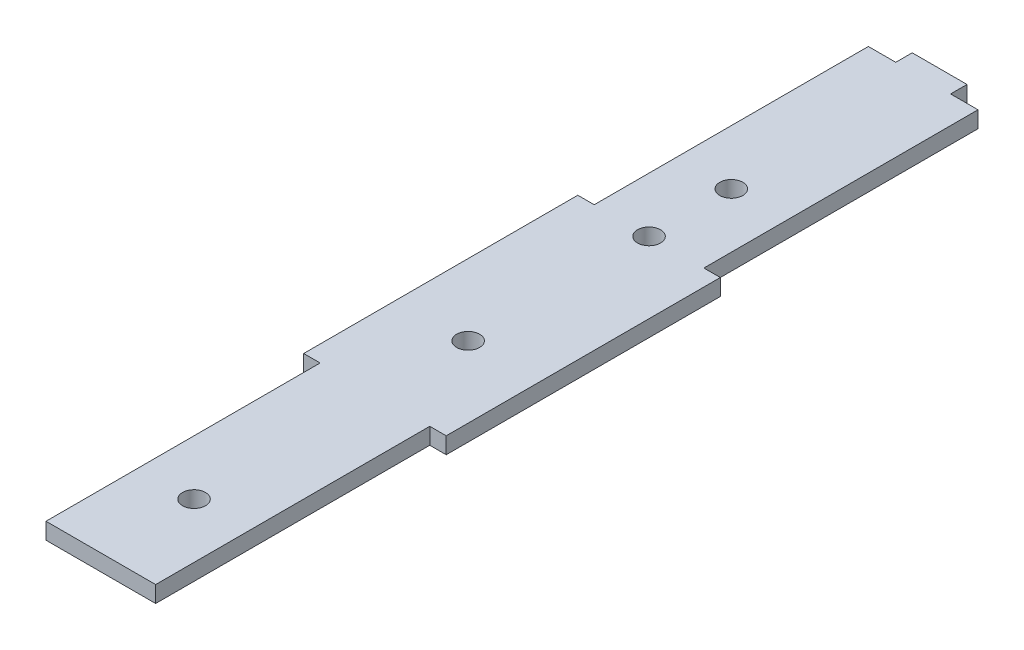
SolidWorks part; units mm, degrees
ref_plane "Front Plane" through (0, 0, 0) normal (0, 0, 1) x (1, 0, 0)
ref_plane "Top Plane" through (0, 0, 0) normal (0, 1, 0) x (1, 0, 0)
ref_plane "Right Plane" through (0, 0, 0) normal (1, 0, 0) x (0, 0, -1)
sketch "Sketch1" plane through (0, 0, 0) normal (0, 1, 0) x (1, 0, 0)
  line L0 (15, 0) -> (20, 0)
  line L1 (0, 0) -> (5, 0)
  line L2 (0, 0) -> (0, -50)
  line L3 (0, -150) -> (20, -150)
  line L4 (20, 0) -> (20, -50)
  line L5 (0, -50) -> (-3, -50)
  line L7 (0, -100) -> (-3, -100)
  line L8 (-3, -50) -> (-3, -100)
  line L9 (20, -50) -> (23, -50)
  line L11 (20, -100) -> (23, -100)
  line L12 (23, -50) -> (23, -100)
  line L13 (5, 3) -> (15, 3)
  line L14 (5, 3) -> (5, 0)
  line L16 (15, 3) -> (15, 0)
  line L17 (0, -100) -> (0, -150)
  line L18 (20, -100) -> (20, -150)
  dimension "D1" = 20
  dimension "D2" = 150
  dimension "D3" = 3
  dimension "D4" = 10
  dimension "D5" = 50
extrude "Boss-Extrude1" add sketch "Sketch1" along normal blind 3
sketch "Sketch2" plane through (0, 3, 0) normal (0, 1, 0) x (1, 0, 0)
  line L0 (10, 3) -> (10, -150) construction
  line L1 (15, 3) -> (5, 3) construction
  line L2 (0, -150) -> (20, -150) construction
  line L3 (5, 0) -> (0, 0) construction
  circle A0 centre (10, -35) radius 2.1
  circle A1 centre (10, -50) radius 2.1
  circle A2 centre (10, -83) radius 2.1
  circle A3 centre (10, -133) radius 2.1
  point P16 (10, -43.3835)
  point P17 (10, -111.5459)
  dimension "D1" = 4.2
  dimension "D2" = 35
  dimension "D3" = 15
  dimension "D4" = 50
  dimension "D5" = 33
extrude "Cut-Extrude1" cut sketch "Sketch2" against normal through all
